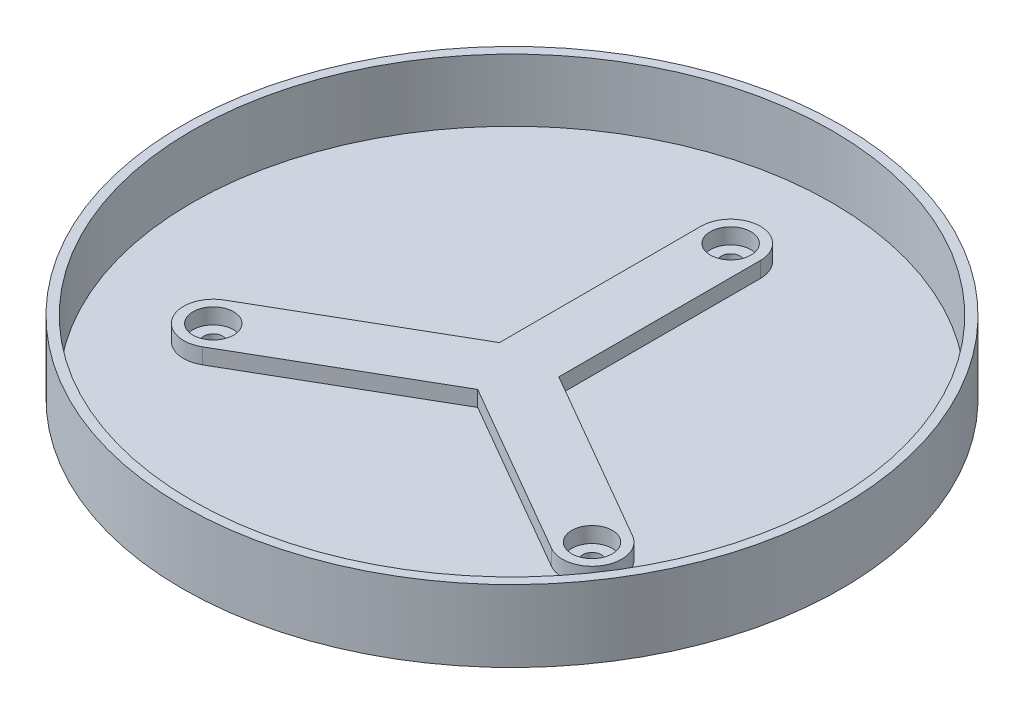
SolidWorks part; units mm, degrees
material "ABS"
ref_plane "Front Plane" through (0, 0, 0) normal (0, 0, 1) x (1, 0, 0)
ref_plane "Top Plane" through (0, 0, 0) normal (0, 1, 0) x (1, 0, 0)
ref_plane "Right Plane" through (0, 0, 0) normal (1, 0, 0) x (0, 0, -1)
sketch "Sketch1" plane through (0, 0, 0) normal (0, 1, 0) x (1, 0, 0)
  circle A0 centre (0, 0) radius 102.5
  dimension "D1" = 205
extrude "Boss-Extrude2" add sketch "Sketch1" along normal blind 20 contours A0
shell "Shell3" thickness 3
sketch "Sketch3" plane through (0, 0, 0) normal (0, 1, 0) x (1, 0, 0)
  line L0 (-9.5, 70) -> (-9.5, -4.6188)
  line L2 (9.5, -4.6188) -> (9.5, 70)
  line L3 (-8.75, -5.9178) -> (55.8718, -43.2272)
  line L4 (65.3718, -26.7728) -> (0.75, 10.5366)
  line L5 (-0.75, 10.5366) -> (-65.3718, -26.7728)
  line L6 (-55.8718, -43.2272) -> (8.75, -5.9178)
  line L7 (0, 0) -> (-9.5, -4.6188) construction
  circle A0 centre (0, 70) radius 6.5
  arc A1 (9.5, 70) -> (-9.5, 70) centre (0, 70) ccw
  circle A6 centre (0, 0) radius 102.5 construction
  circle A7 centre (60.6218, -35) radius 6.5
  arc A8 (55.8718, -43.2272) -> (65.3718, -26.7728) centre (60.6218, -35) ccw
  circle A9 centre (-60.6218, -35) radius 6.5
  arc A10 (-65.3718, -26.7728) -> (-55.8718, -43.2272) centre (-60.6218, -35) ccw
  point P21 (0, -4.6188)
  dimension "D2" = 13
  dimension "D3" = 3
  dimension "D5" = 10.5633
  dimension "D6" = 55.8718
  dimension "D1" = 70
  dimension "D4" = 3
extrude "Boss-Extrude8" add sketch "Sketch3" along normal blind 5
sketch "Sketch5" plane through (0, 0, 0) normal (0, 1, 0) x (1, 0, 0)
  circle A0 centre (0, 70) radius 3
  circle A1 centre (60.6218, -35) radius 3
  circle A2 centre (-60.6218, -35) radius 3
  point P9 (0, 0)
  dimension "D1" = 6
  dimension "D2" = 70
  dimension "D3" = 3
extrude "Cut-Extrude2" cut sketch "Sketch5" against normal through all both and the other way through all
